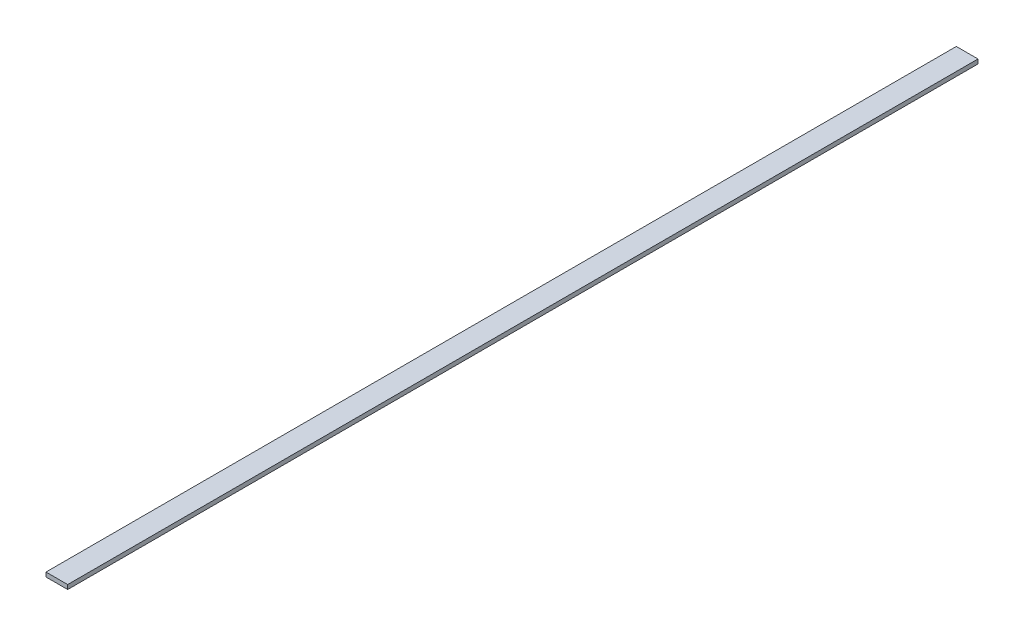
SolidWorks part; units mm, degrees
ref_plane "Face" through (0, 0, 0) normal (0, 0, 1) x (1, 0, 0)
ref_plane "Dessus" through (0, 0, 0) normal (0, 1, 0) x (1, 0, 0)
ref_plane "Droite" through (0, 0, 0) normal (1, 0, 0) x (0, 0, -1)
sketch "Esquisse1" plane through (0, 0, 0) normal (0, 1, 0) x (1, 0, 0)
  line L1 (0, 0) -> (50, 0)
  line L2 (0, 0) -> (0, 2100)
  line L3 (0, 2100) -> (50, 2100)
  line L4 (50, 0) -> (50, 2100)
  dimension "D1" = 50
  dimension "D2" = 2100
extrude "Extrusion1" add sketch "Esquisse1" along normal blind 10
